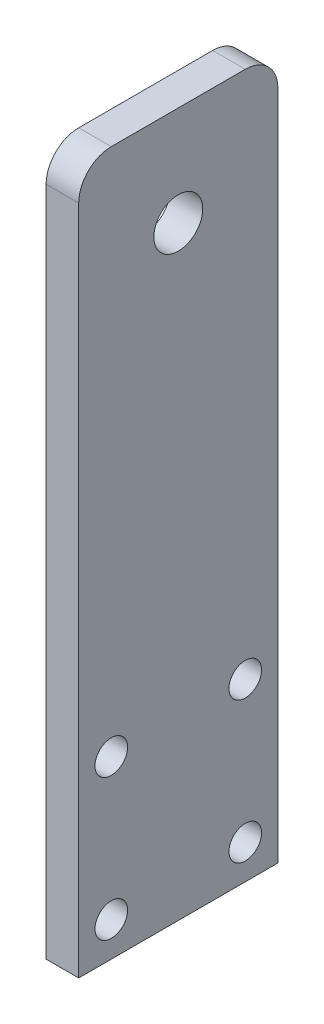
SolidWorks part; units mm, degrees
ref_plane "Front Plane" through (0, 0, 0) normal (0, 0, 1) x (1, 0, 0)
ref_plane "Top Plane" through (0, 0, 0) normal (0, 1, 0) x (1, 0, 0)
ref_plane "Right Plane" through (0, 0, 0) normal (1, 0, 0) x (0, 0, -1)
sketch "Sketch1" plane through (0, 0, 0) normal (1, 0, 0) x (0, 0, -1)
  line L0 (-19.4, 20.4391) -> (-19.4, 77.8465)
  line L2 (19.4, 77.8465) -> (19.4, 20.4391)
  line L3 (19.4, 116.6465) -> (-19.4, 116.6465)
  line L4 (19.4, 116.6465) -> (19.4, 77.8465)
  line L5 (19.4, 77.8465) -> (-19.4, 77.8465) construction
  line L6 (-19.4, 116.6465) -> (-19.4, 77.8465)
  line L7 (19.4, 116.6465) -> (-19.4, 77.8465) construction
  line L8 (19.4, 77.8465) -> (-19.4, 116.6465) construction
  circle A0 centre (0, 97.2465) radius 4.7625
  point P7 (0, 97.2465)
  line B0 (-19.4, 20.4391) -> (19.4, -20.4391) construction
  line B1 (19.4, 20.4391) -> (-19.4, -20.4391) construction
  line B2 (-19.4, -20.4391) -> (19.4, -20.4391)
  line B3 (19.4, -20.4391) -> (19.4, 20.4391)
  line B4 (19.4, 20.4391) -> (-19.4, 20.4391)
  line B5 (-19.4, 20.4391) -> (-19.4, -20.4391)
  circle B6 centre (-13.05, 13.749) radius 3.175
  arc B7 (0.1268, 92.4856) -> (-0.0042, 102.009) centre (0, 97.2465) ccw
  circle B8 centre (13.05, 13.749) radius 3.175
  circle B9 centre (-13.05, -13.749) radius 3.175
  circle B10 centre (13.05, -13.749) radius 3.175
  spline B11 degree 3 poles (-0.0042, 102.009) (0.0014, 101.9922) (0.0011, 101.9736) (-0.0103, 101.9401) (-0.0206, 101.9253) (-0.0559, 101.8858) (-0.0846, 101.8657) (-0.1739, 101.81) (-0.2371, 101.7808) (-0.4281, 101.6961) (-0.558, 101.6453) (-0.9442, 101.4851) (-1.1975, 101.3699) (-1.6858, 101.1022) (-1.9218, 100.9499) (-2.3604, 100.6129) (-2.5647, 100.4276) (-2.9411, 100.0208) (-3.1138, 99.7975) (-3.4102, 99.3313) (-3.5361, 99.0866) (-3.7392, 98.5719) (-3.8169, 98.2998) (-3.9165, 97.7549) (-3.94, 97.4794) (-3.9335, 96.9225) (-3.903, 96.6429) (-3.7903, 96.1014) (-3.7082, 95.8365) (-3.4897, 95.3199) (-3.3565, 95.0767) (-3.048, 94.6171) (-2.8706, 94.399) (-2.4823, 93.9998) (-2.2724, 93.819) (-1.8239, 93.4923) (-1.5837, 93.3461) (-1.0876, 93.0911) (-0.8299, 92.9824) (-0.4381, 92.8327) (-0.3064, 92.7856) (-0.1121, 92.7065) (-0.0474, 92.679) (0.043, 92.6266) (0.0727, 92.6069) (0.1084, 92.5688) (0.1189, 92.5542) (0.1311, 92.5212) (0.1318, 92.5026) (0.1268, 92.4856) knots 0 0 0 0 0.003906 0.003906 0.007812 0.007812 0.015625 0.015625 0.03125 0.03125 0.0625 0.0625 0.125 0.125 0.1875 0.1875 0.25 0.25 0.3125 0.3125 0.375 0.375 0.4375 0.4375 0.5 0.5 0.5625 0.5625 0.625 0.625 0.6875 0.6875 0.75 0.75 0.8125 0.8125 0.875 0.875 0.9375 0.9375 0.96875 0.96875 0.984375 0.984375 0.992188 0.992188 0.996094 0.996094 1 1 1 1
sketch_block_instance "Block-LateralMotorPlate-1"
sketch_block "Block-LateralMotorPlate" parameters "D2"=6.35, "D1"=6.35
extrude "Boss-Extrude1" add sketch "Sketch1" along normal blind 6.35 contours B4 L2 L4 L3 L6 L0 A0 | B4 B5 B2 B3 B10 B9 B8 B6
fillet "Fillet1" radius 6.35 2 edges at (3.175, 116.6465, 19.4) (3.175, 116.6465, -19.4)
